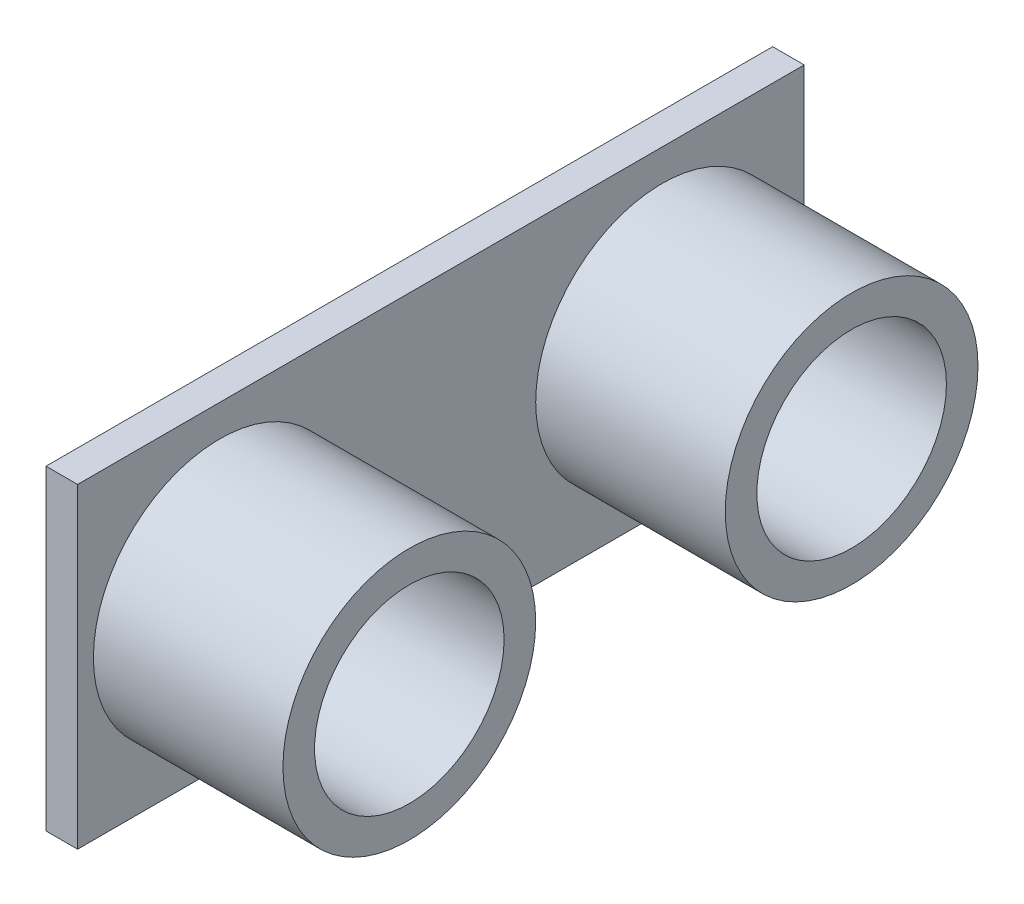
SolidWorks part; units mm, degrees
ref_plane "Front Plane" through (0, 0, 0) normal (0, 0, 1) x (1, 0, 0)
ref_plane "Top Plane" through (0, 0, 0) normal (0, 1, 0) x (1, 0, 0)
ref_plane "Right Plane" through (0, 0, 0) normal (1, 0, 0) x (0, 0, -1)
sketch "Sketch1" plane through (0, 0, 0) normal (1, 0, 0) x (0, 0, -1)
  line L1 (0, 0) -> (46, 0)
  line L2 (0, 0) -> (0, 20)
  line L3 (0, 20) -> (46, 20)
  line L4 (46, 0) -> (46, 20)
  dimension "D1" = 46
  dimension "D2" = 20
extrude "Boss-Extrude1" add sketch "Sketch1" along normal mid plane 2
sketch "Sketch2" plane through (1, 0, 0) normal (1, 0, 0) x (0, 0, -1)
  line L0 (0, 20) -> (0, 0) construction
  line L1 (0, 0) -> (46, 0) construction
  line L2 (46, 0) -> (46, 20) construction
  circle A0 centre (9, 10) radius 8
  circle A1 centre (37, 10) radius 8
  circle A2 centre (9, 10) radius 6
  circle A3 centre (37, 10) radius 6
  dimension "D1" = 16
  dimension "D4" = 10
  dimension "D6" = 12
  dimension "D2" = 9
  dimension "D3" = 10
  dimension "D5" = 9
extrude "Boss-Extrude2" add sketch "Sketch2" along normal blind 12
sketch "Sketch3" plane through (-1, 0, 0) normal (-1, 0, 0) x (0, 0, 1)
  line L0 (0, 0) -> (-46, 0) construction
  line L1 (-25.4273, 1.4471) -> (-19.5457, 1.4471)
  line L2 (-25.4273, 1.4471) -> (-25.4273, 0)
  line L3 (-25.4273, 0) -> (-19.5457, 0)
  line L4 (-19.5457, 1.4471) -> (-19.5457, 0)
  point P6 (-23, 0)
extrude "Boss-Extrude3" add sketch "Sketch3" along normal blind 5
